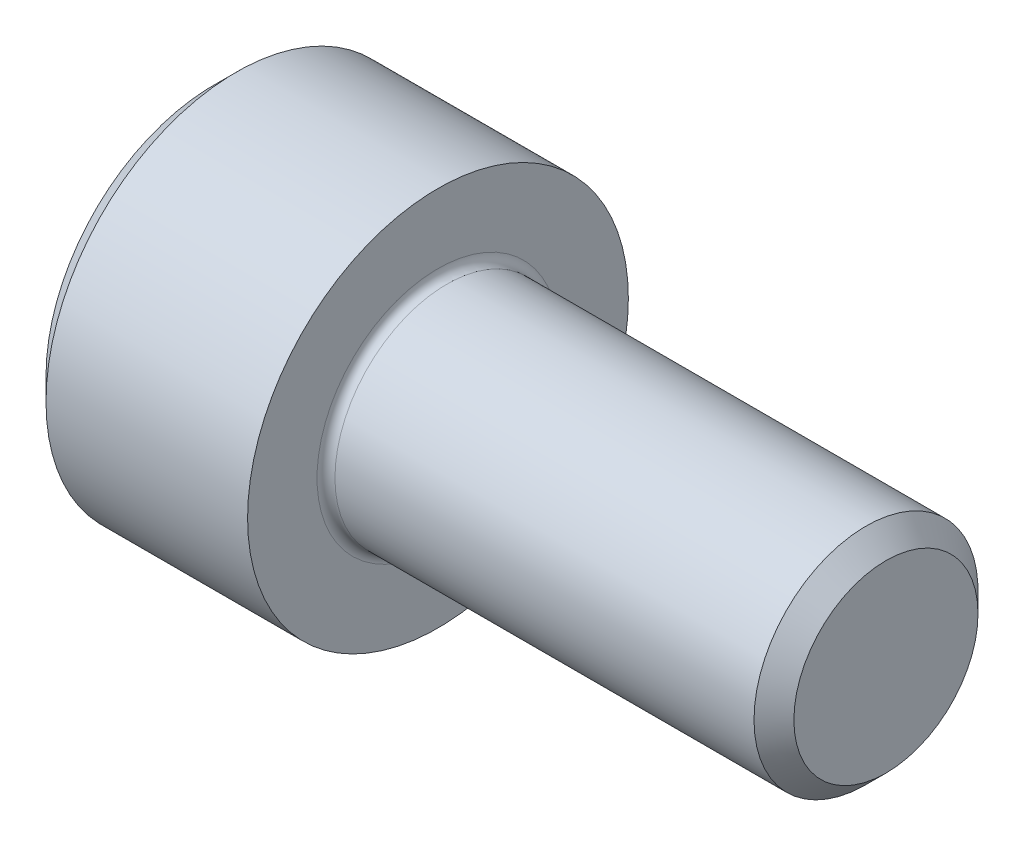
SolidWorks part; units mm, degrees
ref_plane "Plane1" through (0, 0, 0) normal (0, 0, 1) x (1, 0, 0)
ref_plane "Plane2" through (0, 0, 0) normal (0, 1, 0) x (1, 0, 0)
ref_plane "Plane3" through (0, 0, 0) normal (1, 0, 0) x (0, 0, -1)
revolve "Base-Revolve" add sketch "BodySke"
sketch "BodySke" plane through (0, 0, 0) normal (0, 0, 1) x (1, 0, 0)
  line L0 (0, 0) -> (0, 3.75)
  line L1 (0.5, 4.25) -> (5, 4.25)
  line L2 (5, 4.25) -> (5, 2.5)
  line L3 (5, 2.5) -> (14.555, 2.5)
  line L4 (15, 2.055) -> (15, 0)
  line L5 (15, 0) -> (0, 0)
  line L6 (-31.75, 0) -> (127, 0) construction
  line L7 (0, 3.75) -> (0.5, 4.25)
  line L8 (15, 2.055) -> (14.555, 2.5)
  line L9 (0, -3.75) -> (0.5, -4.25) construction
  line L10 (15, -2.055) -> (14.555, -2.5) construction
  line L11 (5.8, 9.525) -> (5.8, 3.175) construction
  line L12 (5, 9.525) -> (5, 3.175) construction
  line L13 (-35, 9.525) -> (-35, 3.175) construction
  dimension "Diameter" = 5
  dimension "Head_ht" = 5
  dimension "Length" = 10
  dimension "Body_ch_ang" = 45
  dimension "Head_dia" = 8.5
  dimension "Head_ch_ang" = 45
  dimension "Minor_dia" = 4.11
  dimension "Advance" = 0.8
  dimension "Thread_nom" = 10
  dimension "Thread_length" = 50
  dimension "Head_ch_ht" = 0.5
cosmetic thread "ThreadCosmetic" [suppressed]
fillet "Fillet1" radius 0.2 1 edges at (5, 0, 2.5)
sketch "Sketch2" plane through (0, 0, 0) normal (0, 0, 1) x (1, 0, 0)
  line L0 (0, 2.042) -> (2.5, 2.042)
  line L1 (2.5, 2.042) -> (3.6789, 0)
  line L2 (-31.75, 0) -> (127, 0) construction
  line L3 (3.6789, 0) -> (0, 0)
  line L4 (0, 0) -> (0, 2.042)
  line L5 (0, 3.75) -> (0, -3.75) construction
  line L6 (0, 0) -> (47.625, 0) construction
  line L7 (5, -4.25) -> (5, 4.25) construction
  dimension "D1" = 2.042
  dimension "D2" = 60
  dimension "Wall_thickness" = 2.5
revolve "Hex-PreBroach" cut sketch "Sketch2" angle 360 about L6
sketch "Sketch3" plane through (0, 0, 0) normal (-1, 0, 0) x (0, 0.5, 0.866)
  line L0 (1.1789, 2.042) -> (-1.1789, 2.042)
  line L1 (-1.1789, 2.042) -> (-2.3579, 0)
  line L2 (1.1789, 2.042) -> (2.3579, 0)
  line L3 (1.1789, -2.042) -> (2.3579, 0)
  line L4 (1.1789, -2.042) -> (-1.1789, -2.042)
  line L5 (-1.1789, -2.042) -> (-2.3579, 0)
  dimension "D1" = 2.042
  dimension "D2" = 2.042
  dimension "Hex_size" = 4.084
extrude "Hex" cut sketch "Sketch3" against normal blind 2.5
sketch "Sketch4" plane through (0, 0, 0) normal (-1, 0, 0) x (0, 0, 1)
  line L0 (0, 0) -> (2.3876, 0)
  line L1 (0, 0) -> (6.1484, 3.5498) construction
  line L2 (0, 0) -> (1.1938, 2.0677)
  line L3 (1.9883, 0.576) -> (2.2704, 0.7389)
  line L4 (1.493, 1.4339) -> (1.7751, 1.5968)
  arc A0 (1.9883, 0.576) -> (1.493, 1.4339) centre (0, 0) ccw
  arc A1 (2.3876, 0) -> (2.2704, 0.7389) centre (0, 0) ccw
  arc A2 (1.1938, 2.0677) -> (1.7751, 1.5968) centre (0, 0) cw
  dimension "D1" = 30
  dimension "Spline_n_dim" = 4.1402
  dimension "Spline_m_dim" = 4.7752
  dimension "D2" = 60
  dimension "D3" = 0.4953
  dimension "Spline_p_dim" = 0.9906
extrude "Spline" [suppressed] cut sketch "Sketch4" against normal blind 2.5
pattern_circular "CirPattern1" [suppressed] count 6 every 60
sketch "Sketch5" plane through (0, 0, 0) normal (0, 0, 1) x (1, 0, 0)
  line L0 (-31.75, 0) -> (127, 0) construction
  line L2 (0, 3.75) -> (0, -3.75) construction
  circle A0 centre (2, 0) radius 0.675
  dimension "Drilled_hole_dia" = 1.35
  dimension "Drilled_hole_loc" = 2
extrude "Hole" [suppressed] cut sketch "Sketch5" against normal through all and the other way through all
pattern_circular "Drilled-4" [suppressed] count 2 every 60
pattern_circular "Drilled-6" [suppressed] count 3 every 60
sketch "ThdSchSke" plane through (0, 0, 0) normal (0, 0, 1) x (1, 0, 0)
  line L0 (5.8, -2.055) -> (5.4884, -2.5)
  line L1 (5.8, -2.055) -> (6.1116, -2.5)
  line L2 (6.1116, -2.5) -> (6.1116, -3.125)
  line L3 (-3.175, 0) -> (5.1513, 0) construction
  line L5 (6.1116, -3.125) -> (5.4884, -3.125)
  line L6 (5.4884, -3.125) -> (5.4884, -2.5)
  line L7 (0, 3.75) -> (0, -3.75) construction
  dimension "Thread_minor" = 4.11
  dimension "Diameter" = 5
  dimension "Start" = 5.8
  dimension "SideAngle" = 55
  dimension "VeeAngle" = 70
  dimension "Overcut" = 6.25
revolve "ThreadSchematic" [suppressed] cut sketch "ThdSchSke" angle 360 about L3
pattern_linear "ThdSchPat" [suppressed]
equation "\"D2@Sketch3\" = \"Hex_size@Sketch3\" / 2"
equation "\"D1@Sketch3\" = \"Hex_size@Sketch3\" / 2"
equation "\"D1@Sketch2\" = \"Hex_size@Sketch3\" / 2"
equation "\"D3@Sketch4\" = \"Spline_p_dim@Sketch4\" / 2"
equation "\"Thread_minor@ThreadCosmetic\"  =  \"Minor_dia@BodySke\""
equation "\"D2@CirPattern1\" = 360 / \"Num_teeth@CirPattern1\""
equation "\"Wall_thickness@Sketch2\" = \"Head_ht@BodySke\" - \"Key_eng@Hex\""
equation "\"Thread_length@ThreadCosmetic\" = ((sgn( (\"Length@BodySke\" - \"Advance@BodySke\" ) - \"Thread_nom@BodySke\" )-1)*( (\"Length@BodySke\" - \"Advance@BodySke\" ) - \"Thread_nom@BodySke\" ))/-2+ \"Thread_nom@BodySke\""
equation "\"Thread_minor@ThdSchSke\" = \"Minor_dia@BodySke\""
equation "\"Diameter@ThdSchSke\" = \"Diameter@BodySke\""
equation "\"Overcut@ThdSchSke\" = \"Diameter@BodySke\" * 1.25"
equation "\"Start@ThdSchSke\" = \"Head_ht@BodySke\" + \"Length@BodySke\" - \"Thread_length@ThreadCosmetic\"  '---Non-countersunk---"
equation "\"Num_threads@ThdSchPat\" = int( \"Thread_length@ThreadCosmetic\" / \"Advance@BodySke\" + 0.999 )  + 1"
equation "\"Advance@ThdSchPat\" = \"Thread_length@ThreadCosmetic\" /  (\"Num_threads@ThdSchPat\" - 1) 'relax it"
equation "\"Num_threads@ThdSchPat\" = \"Num_threads@ThdSchPat\" - sgn( \"Num_threads@ThdSchPat\" - 1) '---chamfered tips only---"
